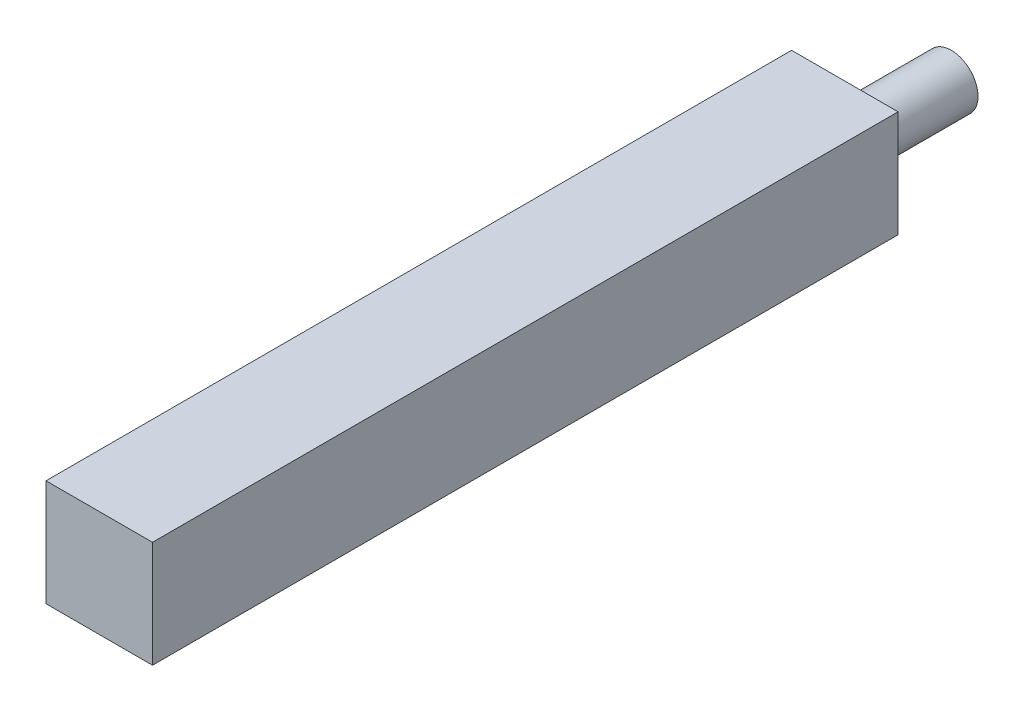
SolidWorks part; units mm, degrees
ref_plane "Front Plane" through (0, 0, 0) normal (0, 0, 1) x (1, 0, 0)
ref_plane "Top Plane" through (0, 0, 0) normal (0, 1, 0) x (1, 0, 0)
ref_plane "Right Plane" through (0, 0, 0) normal (1, 0, 0) x (0, 0, -1)
sketch "Sketch1" plane through (0, 0, 0) normal (0, 0, 1) x (1, 0, 0)
  line L0 (0, 0) -> (100, 0)
  line L1 (100, 0) -> (100, 100)
  line L2 (100, 100) -> (0, 100)
  line L3 (0, 100) -> (0, 0)
  dimension "D1" = 100
  dimension "D2" = 100
extrude "Boss-Extrude1" add sketch "Sketch1" along normal blind 700
sketch "Sketch2" plane through (0, 0, 0) normal (0, 0, 1) x (1, 0, 0)
  line L0 (50, 100) -> (50, 0)
  line L1 (100, 100) -> (0, 100) construction
  line L2 (0, 0) -> (100, 0) construction
  circle A0 centre (50, 50) radius 25
extrude "Boss-Extrude2" add sketch "Sketch2" against normal blind 100 contours A0
